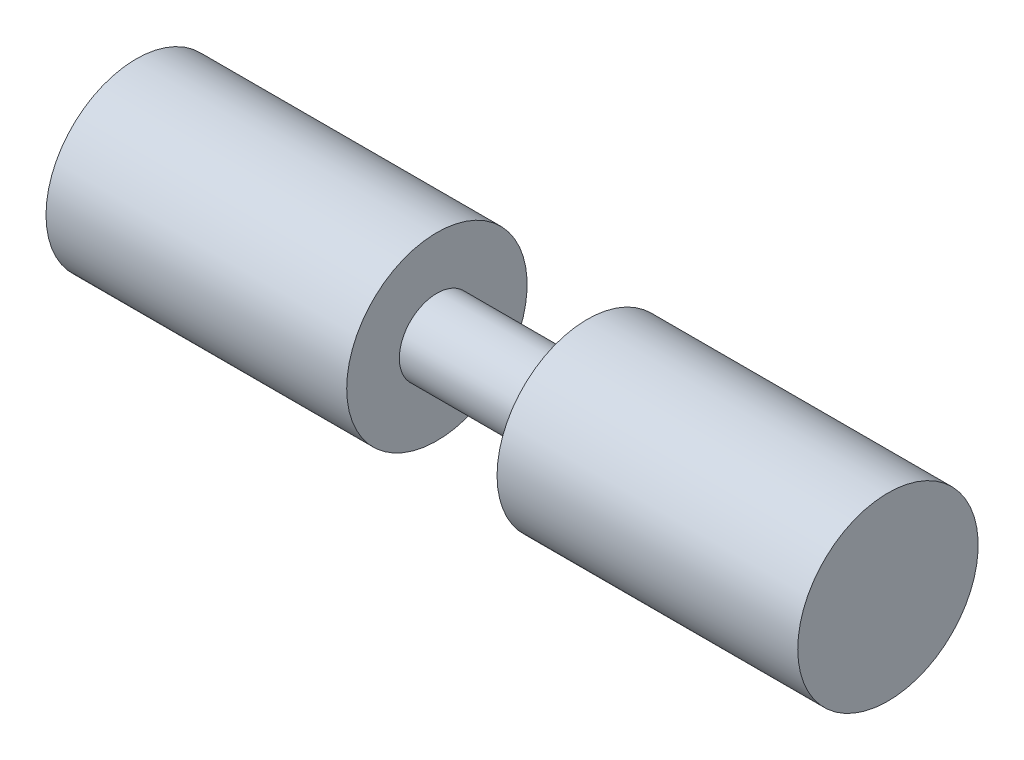
SolidWorks part; units mm, degrees
ref_plane "Front Plane" through (0, 0, 0) normal (0, 0, 1) x (1, 0, 0)
ref_plane "Top Plane" through (0, 0, 0) normal (0, 1, 0) x (1, 0, 0)
ref_plane "Right Plane" through (0, 0, 0) normal (1, 0, 0) x (0, 0, -1)
sketch "Sketch1" plane through (0, 0, 0) normal (0, 0, 1) x (1, 0, 0)
  line L0 (0, 0) -> (127, 0) construction
  line L1 (0, 0) -> (0, 15.24)
  line L2 (0, 15.24) -> (50.8, 15.24)
  line L3 (50.8, 15.24) -> (50.8, 6.35)
  line L4 (50.8, 6.35) -> (76.2, 6.35)
  line L5 (76.2, 6.35) -> (76.2, 15.24)
  line L6 (76.2, 15.24) -> (127, 15.24)
  line L7 (127, 15.24) -> (127, 0)
  line L8 (0, 0) -> (127, 0)
  dimension "D1" = 25.4
  dimension "D2" = 6.35
  dimension "D3" = 15.24
  dimension "D4" = 50.8
revolve "Revolve1" add sketch "Sketch1" angle 360 about L0
